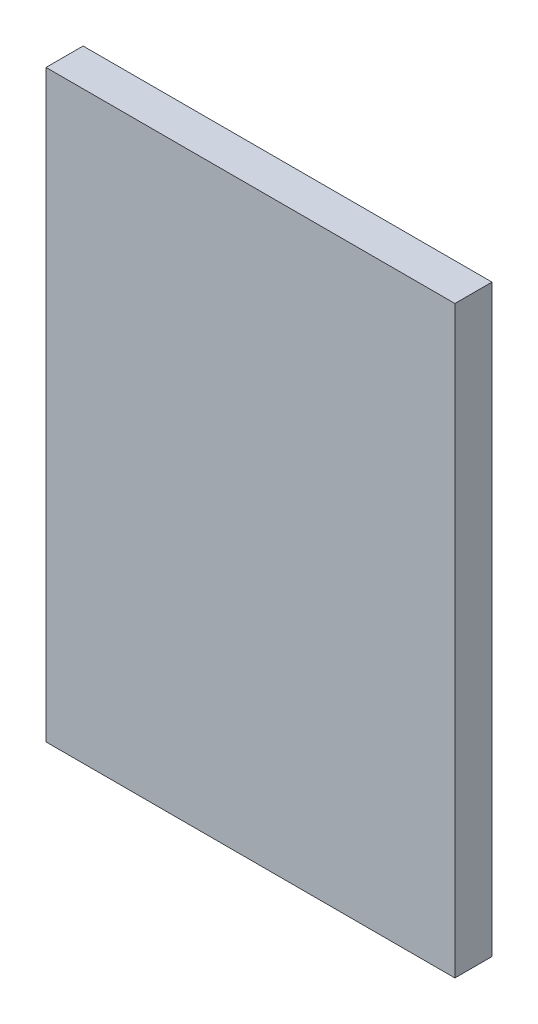
SolidWorks part; units mm, degrees
ref_plane "Front Plane" through (0, 0, 0) normal (0, 0, 1) x (1, 0, 0)
ref_plane "Top Plane" through (0, 0, 0) normal (0, 1, 0) x (1, 0, 0)
ref_plane "Right Plane" through (0, 0, 0) normal (1, 0, 0) x (0, 0, -1)
sketch "Sketch1" plane through (0, 0, 0) normal (0, 0, 1) x (1, 0, 0)
  line L1 (-17.5, -25) -> (17.5, -25)
  line L2 (-17.5, -25) -> (-17.5, 25)
  line L3 (-17.5, 25) -> (17.5, 25)
  line L4 (17.5, -25) -> (17.5, 25)
  line L5 (-17.5, -25) -> (17.5, 25) construction
  line L6 (-17.5, 25) -> (17.5, -25) construction
  point P0 (0, 0)
  dimension "D1" = 35
  dimension "D2" = 50
extrude "Boss-Extrude1" add sketch "Sketch1" along normal blind 3.175
